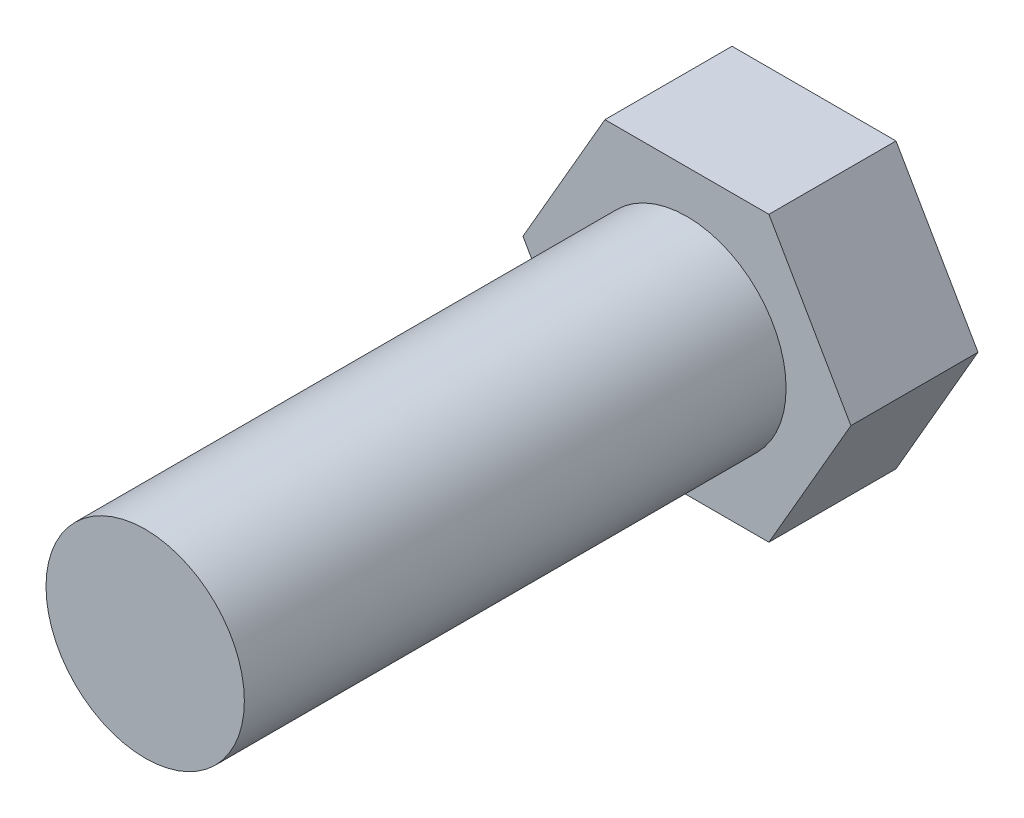
SolidWorks part; units mm, degrees
ref_plane "Alzado" through (0, 0, 0) normal (0, 0, 1) x (1, 0, 0)
ref_plane "Planta" through (0, 0, 0) normal (0, 1, 0) x (1, 0, 0)
ref_plane "Vista lateral" through (0, 0, 0) normal (1, 0, 0) x (0, 0, -1)
sketch "Sketch1" plane through (0, 0, 0) normal (0, 0, 1) x (1, 0, 0)
  line L1 (1.9675, -3.4078) -> (3.935, 0)
  line L2 (3.935, 0) -> (1.9675, 3.4078)
  line L3 (1.9675, 3.4078) -> (-1.9675, 3.4078)
  line L4 (-1.9675, 3.4078) -> (-3.935, 0)
  line L5 (-3.935, 0) -> (-1.9675, -3.4078)
  line L6 (-1.9675, -3.4078) -> (1.9675, -3.4078)
  circle A0 centre (0, 0) radius 3.4078 construction
  dimension "D1" = 7.87
extrude "Boss-Extrude1" add sketch "Sketch1" along normal blind 3.05
sketch "Sketch2" plane through (0, 0, 3.05) normal (0, 0, 1) x (1, 0, 0)
  circle A0 centre (0, 0) radius 2.38
  dimension "D1" = 4.76
extrude "Boss-Extrude2" add sketch "Sketch2" along normal blind 13
